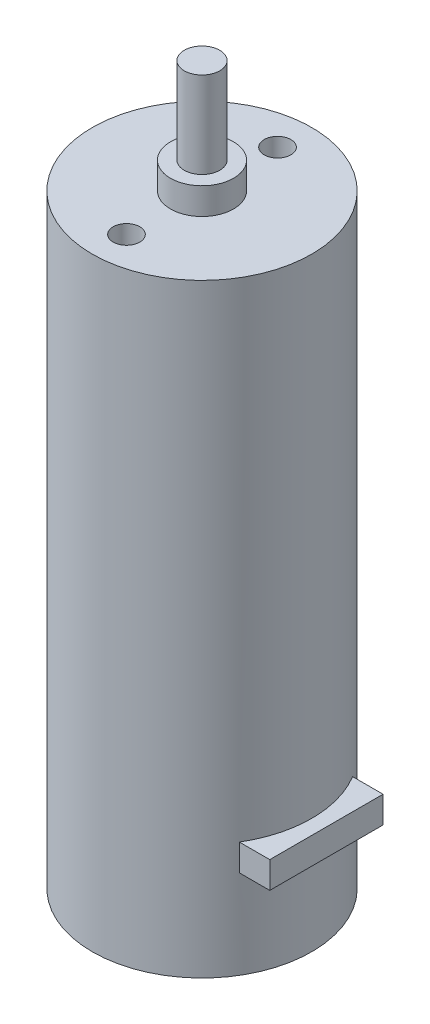
SolidWorks part; units mm, degrees
material "1060 Alloy"
ref_plane "Front Plane" through (0, 0, 0) normal (0, 0, 1) x (1, 0, 0)
ref_plane "Top Plane" through (0, 0, 0) normal (0, 1, 0) x (1, 0, 0)
ref_plane "Right Plane" through (0, 0, 0) normal (1, 0, 0) x (0, 0, -1)
sketch "Sketch1" plane through (0, 0, 0) normal (0, 1, 0) x (1, 0, 0)
  circle A0 centre (0, 0) radius 12.35
  dimension "D1" = 24.7
extrude "Boss-Extrude1" add sketch "Sketch1" along normal blind 68
sketch "Sketch2" plane through (0, 68, 0) normal (0, 1, 0) x (1, 0, 0)
  circle A0 centre (0, 0) radius 3.55
  dimension "D1" = 7.1
extrude "Boss-Extrude2" add sketch "Sketch2" along normal blind 3
sketch "Sketch3" plane through (0, 71, 0) normal (0, 1, 0) x (1, 0, 0)
  circle A0 centre (0, 0) radius 2
  dimension "D1" = 4
extrude "Boss-Extrude3" add sketch "Sketch3" along normal blind 9.7
sketch "Sketch4" plane through (0, 68, 0) normal (0, 1, 0) x (1, 0, 0)
  circle A0 centre (0, 8.5) radius 1.5
  circle A1 centre (0, 0) radius 12.35 construction
  circle A2 centre (0, -8.5) radius 1.5
  point P6 (0, 0)
  point P8 (0, 0)
  dimension "D2" = 3
  dimension "D1" = 8.5
  dimension "D3" = 8.5
sketch "Sketch5" plane through (0, 0, 0) normal (1, 0, 0) x (0, 0, -1)
  line L1 (-6.375, 13) -> (6.375, 13)
  line L2 (-6.375, 13) -> (-6.375, 10)
  line L3 (-6.375, 10) -> (6.375, 10)
  line L4 (6.375, 13) -> (6.375, 10)
  line L5 (-6.375, 13) -> (6.375, 10) construction
  line L6 (-6.375, 10) -> (6.375, 13) construction
  line L7 (-12.35, 0) -> (12.35, 0) construction
  point P0 (0, 11.5)
  point P5 (0, 0)
  dimension "D1" = 10
  dimension "D2" = 12.75
  dimension "D3" = 3
extrude "Boss-Extrude4" add sketch "Sketch5" along normal blind 14
extrude "Cut-Extrude1" cut sketch "Sketch4" against normal blind 3 contours A0 | A2
